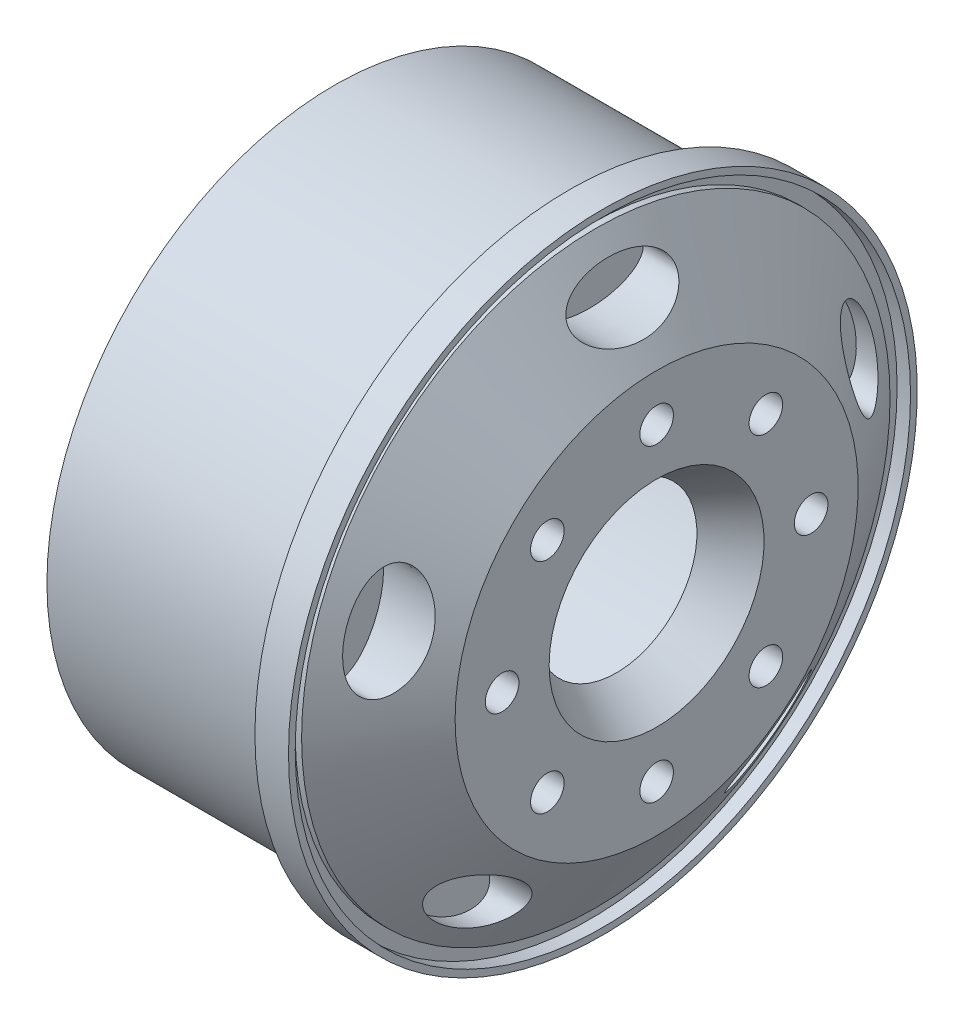
SolidWorks part; units mm, degrees
ref_plane "Front Plane" through (0, 0, 0) normal (0, 0, 1) x (1, 0, 0)
ref_plane "Top Plane" through (0, 0, 0) normal (0, 1, 0) x (1, 0, 0)
ref_plane "Right Plane" through (0, 0, 0) normal (1, 0, 0) x (0, 0, -1)
sketch "Sketch3" plane through (0, 0, 0) normal (0, 1, 0) x (1, 0, 0)
  line L0 (-29.7742, 0) -> (36.8095, 0) construction
  line L2 (10.3693, 23.4) -> (8.8693, 23.4)
  line L7 (8.8693, 23.4) -> (8.8693, 21.4)
  line L8 (8.8693, 21.4) -> (-8.6107, 21.4)
  line L9 (-8.6107, 21.4) -> (-8.6107, 18.2319)
  line L10 (10.3693, 23.4) -> (11.3693, 23.4)
  line L11 (11.3693, 23.4) -> (11.3693, 22.9)
  line L12 (11.3693, 22.9) -> (10.3693, 22.9)
  line L13 (10.8435, 21.9) -> (15.3693, 15)
  line L14 (15.3693, 15) -> (15.3693, 8)
  line L16 (-8.6107, 18.2319) -> (9.2115, 18.2319)
  line L17 (9.2115, 18.2319) -> (12.3693, 13.4176)
  line L18 (12.3693, 13.4176) -> (12.3693, 6)
  line L20 (12.3693, 6) -> (15.3693, 8)
  line L21 (10.3693, 22.9) -> (10.3693, 21.9)
  line L22 (10.3693, 21.9) -> (10.8435, 21.9)
  dimension "D1" = 1.5
  dimension "D2" = 46.8
  dimension "D3" = 2
  dimension "D4" = 42.8
  dimension "D5" = 18.98
  dimension "D6" = 1
  dimension "D7" = 0.5
  dimension "D8" = 30
  dimension "D9" = 5
  dimension "D10" = 3
  dimension "D11" = 1
  dimension "D12" = 20.98
  dimension "D13" = 13.4176
  dimension "D14" = 123.261
  dimension "D15" = 18.2319
  dimension "D16" = 12
revolve "Revolve1" add sketch "Sketch3" angle 360 about L0
sketch "Sketch4" plane through (15.3693, 0, 0) normal (1, 0, 0) x (0, 0, -1)
  circle A0 centre (0, 0) radius 11.5 construction
  circle A1 centre (0, 11.5) radius 1.25
  circle A2 centre (8.1317, 8.1317) radius 1.25
  circle A3 centre (11.5, 0) radius 1.25
  circle A4 centre (8.1317, -8.1317) radius 1.25
  circle A5 centre (0, -11.5) radius 1.25
  circle A6 centre (-8.1317, -8.1317) radius 1.25
  circle A7 centre (-11.5, 0) radius 1.25
  circle A8 centre (0, 0) radius 18.5 construction
  circle A9 centre (-8.1317, 8.1317) radius 1.25
  ellipse E0 centre (0, 18.5) end of major axis (4, 18.5) minor radius 2
  ellipse E1 centre (17.5945, 5.7168) end of major axis (18.8306, 1.9126) minor radius 2
  ellipse E2 centre (10.874, -14.9668) end of major axis (7.638, -17.318) minor radius 2
  ellipse E3 centre (-10.874, -14.9668) end of major axis (-14.1101, -12.6157) minor radius 2
  ellipse E4 centre (-17.5945, 5.7168) end of major axis (-16.3585, 9.521) minor radius 2
  point P20 (0, 0)
  point P52 (0, 0)
  dimension "D1" = 23
  dimension "D2" = 2.5
  dimension "D4" = 37
  dimension "D5" = 8
  dimension "D6" = 4
  dimension "D3" = 8
  dimension "D7" = 5
extrude "Cut-Extrude1" cut sketch "Sketch4" against normal blind 5
